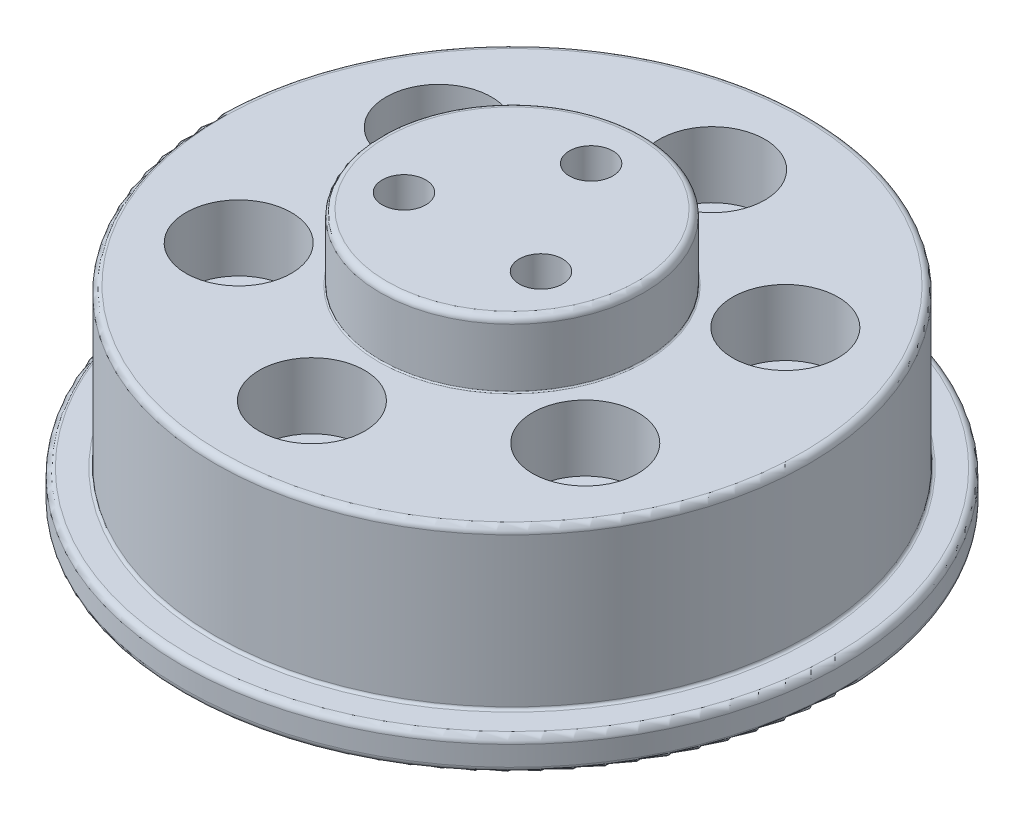
SolidWorks part; units mm, degrees
material "7075-T6, 플레이트 (SS)"
ref_plane "정면" through (0, 0, 0) normal (0, 0, 1) x (1, 0, 0)
ref_plane "윗면" through (0, 0, 0) normal (0, 1, 0) x (1, 0, 0)
ref_plane "우측면" through (0, 0, 0) normal (1, 0, 0) x (0, 0, -1)
sketch "스케치1" plane through (0, 0, 0) normal (0, 1, 0) x (1, 0, 0)
  circle A0 centre (0, 0) radius 10.1
  dimension "D1" = 20.2
extrude "보스-돌출1" add sketch "스케치1" along normal blind 2.5
sketch "스케치2" plane through (0, 2.5, 0) normal (0, 1, 0) x (1, 0, 0)
  circle A0 centre (0, 0) radius 25
  dimension "D1" = 50
extrude "보스-돌출2" add sketch "스케치2" along normal blind 2.5
sketch "스케치3" plane through (0, 5, 0) normal (0, 1, 0) x (1, 0, 0)
  circle A0 centre (0, 0) radius 22.5
  dimension "D1" = 45
extrude "보스-돌출4" add sketch "스케치3" along normal blind 12 contours A0
sketch "스케치5" plane through (0, 17, 0) normal (0, 1, 0) x (1, 0, 0)
  circle A0 centre (0, 0) radius 10
  circle A1 centre (0, 0) radius 22.5 construction
  dimension "D1" = 20
extrude "보스-돌출5" add sketch "스케치5" along normal blind 5
sketch "스케치6" plane through (0, 17, 0) normal (0, 1, 0) x (1, 0, 0)
  circle A0 centre (0, 0) radius 15.18 construction
  point P3 (0, 15.18)
  dimension "D1" = 30.36
hole_wizard "M4 육각 소켓 머리 캡 나사용 카운터보어1" positions "스케치7" profile "스케치8" counterbore size "M4" standard "ISO" end condition through all
sketch "스케치7" plane through (0, 17, 0) normal (0, 1, 0) x (1, 0, 0)
  point P0 (0, 15.18)
sketch "스케치8" plane through (0, 17, -15.18) normal (1, 0, 0) x (0, 0, 1)
  line L0 (0, 0) -> (0, 17)
  line L1 (0, 17) -> (2.25, 17)
  line L3 (2.25, 17) -> (2.25, 5)
  line L4 (2.25, 5) -> (4, 5)
  line L5 (4, 5) -> (4, 0)
  line L7 (4, 0) -> (0, 0)
  line L11 (0, -6.35) -> (0, 107.95) construction
  dimension "관통 구멍 지름" = 4.5
  dimension "관통 구멍 깊이" = 17
  dimension "카운터보어 지름" = 8
  dimension "카운터보어 깊이" = 5
pattern_circular "원형 패턴1" count 6 over 360 about axis through (0, 0, 0) along (0, 1, 0) of "M4 육각 소켓 머리 캡 나사용 카운터보어1"
sketch "스케치11" plane through (0, 22, 0) normal (0, 1, 0) x (1, 0, 0)
  circle A0 centre (0, 0) radius 6 construction
  point P3 (0, 6)
  dimension "D1" = 12
hole_wizard "M4 탭을 위한 탭 드릴1" positions "스케치12" profile "스케치13" hole size "M4" standard "ISO"
sketch "스케치12" plane through (0, 22, 0) normal (0, 1, 0) x (1, 0, 0)
  point P0 (0, 6)
sketch "스케치13" plane through (0, 22, -6) normal (1, 0, 0) x (0, 0, 1)
  line L0 (0, 0) -> (0, 5.9914)
  line L1 (0, 5.9914) -> (1.65, 5)
  line L2 (1.65, 5) -> (1.65, 0)
  line L5 (1.65, 0) -> (0, 0)
  line L10 (0, 5.9914) -> (-1.65, 5) construction
  line L11 (0, -6.35) -> (0, 107.95) construction
  dimension "구멍 지름" = 3.3
  dimension "구멍 깊이" = 5
  dimension "드릴 각도" = 118
pattern_circular "원형 패턴2" count 3 over 360 about axis through (0, 0, 0) along (0, 1, 0) of "M4 탭을 위한 탭 드릴1"
fillet "필렛1" radius 0.5 5 edges at (0, 0, 10.1) (0, 2.5, 10.1) (0, 2.5, 25) (0, 5, 25) (0, 17, 22.5)
fillet "필렛2" radius 0.2 1 edges at (0, 5, 22.5)
fillet "필렛3" radius 0.1 1 edges at (0, 17, 10)
fillet "필렛4" radius 0.5 1 edges at (0, 22, 10)
